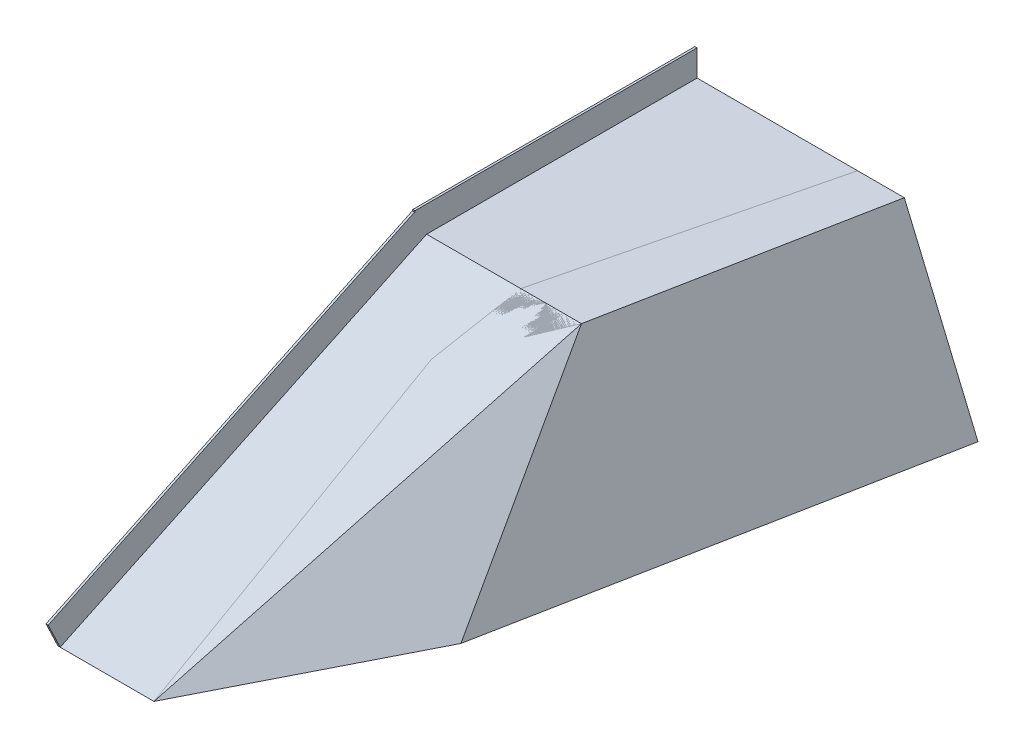
SolidWorks part; units mm, degrees
ref_plane "Front Plane" through (0, 0, 0) normal (0, 0, 1) x (1, 0, 0)
ref_plane "Top Plane" through (0, 0, 0) normal (0, 1, 0) x (1, 0, 0)
ref_plane "Right Plane" through (0, 0, 0) normal (1, 0, 0) x (0, 0, -1)
sketch "Sketch1" plane through (0, 0, 0) normal (0, 1, 0) x (1, 0, 0)
  line L0 (0, 1066.8) -> (0, 0)
  line L1 (0, 0) -> (279.4, 0)
  line L2 (279.4, 0) -> (457.2, 1066.8)
  line L3 (457.2, 1066.8) -> (0, 1066.8)
  dimension "D1" = 279.4
  dimension "D2" = 457.2
  dimension "D3" = 1066.8
extrude "Boss-Extrude1" add sketch "Sketch1" along normal blind 508
sketch "Sketch2" plane through (0, 0, 0) normal (-1, 0, 0) x (0, 0, 1)
  line L0 (0, 0) -> (-1066.8, 508)
  line L1 (-1066.8, 508) -> (-1066.8, 732.6724)
  line L2 (-1066.8, 732.6724) -> (0, 732.6724)
  line L3 (0, 732.6724) -> (0, 0)
extrude "Cut-Extrude1" cut sketch "Sketch2" against normal blind 508
sketch "Sketch3" plane through (0, 0, 0) normal (0, -1, 0) x (1, 0, 0)
  line L0 (0, -1066.8) -> (0, -1854.2)
  line L1 (0, -1854.2) -> (609.6, -1854.2)
  line L2 (609.6, -1854.2) -> (457.2, -1066.8)
  line L3 (457.2, -1066.8) -> (0, -1066.8)
  dimension "D1" = 787.4
  dimension "D2" = 609.6
extrude "Boss-Extrude2" add sketch "Sketch3" against normal blind 508
ref_point "Point1"
sketch "Sketch4" plane through (0, 0, 0) normal (0, -1, 0) x (1, 0, 0)
  line L0 (279.4, 0) -> (758.0246, -943.9298)
  line L1 (758.0246, -943.9298) -> (824.1633, -1854.2)
  line L2 (824.1633, -1854.2) -> (609.6, -1854.2)
  line L4 (609.6, -1854.2) -> (473.6054, -1854.2)
  line L5 (473.6054, -1854.2) -> (229.3242, -858.0039)
  line L6 (229.3242, -858.0039) -> (279.4, 0)
extrude "Boss-Extrude3" add sketch "Sketch4" against normal blind 635 separate body
ref_plane "Plane1" through (158.0257, 112.9593, 80.1278) normal (-0.7521, -0.5376, -0.3813) x (-0.3102, -0.2218, 0.9244)
sketch "Sketch5" plane through (158.0257, 112.9593, 80.1278) normal (-0.7521, -0.5376, -0.3813) x (-0.3102, -0.2218, 0.9244)
  line L0 (-393.6646, 703.6256) -> (953.2419, -176.9288)
  line L1 (953.2419, -176.9288) -> (-1326.8428, -923.5564)
  line L2 (-1326.8428, -923.5564) -> (-2274.7883, -628.3267)
  line L3 (-2274.7883, -628.3267) -> (-2325.5283, 172.3758)
  line L4 (-2325.5283, 172.3758) -> (-393.6646, 703.6256)
extrude "Cut-Extrude3" cut sketch "Sketch5" against normal blind 1016
ref_plane "Plane2" through (397.9401, 254.279, 77.0207) normal (0.8317, 0.5314, 0.161) x (0.1356, 0.0867, -0.987)
sketch "Sketch6" plane through (397.9401, 254.279, 77.0207) normal (0.8317, 0.5314, 0.161) x (0.1356, 0.0867, -0.987)
  line L0 (1082.533, 1261.8546) -> (2538.8005, 767.6885)
  line L1 (2538.8005, 767.6885) -> (2437.6041, -1113.0464)
  line L2 (2437.6041, -1113.0464) -> (306.9995, -1023.5801)
  line L3 (306.9995, -1023.5801) -> (1082.533, 1261.8546)
extrude "Cut-Extrude6" cut sketch "Sketch6" along normal blind 508
sketch "Sketch7" plane through (0, 0, 0) normal (0, 0.9029, 0.4299) x (1, 0, 0)
  line L0 (0, 1181.5779) -> (0, 0)
  line L1 (0, 0) -> (1197.0459, 0)
  line L2 (1197.0459, 0) -> (1543.8795, 955.9278)
  line L3 (1543.8795, 955.9278) -> (976.3528, 2301.292)
  line L4 (976.3528, 2301.292) -> (0, 1181.5779)
extrude "Cut-Extrude7" cut sketch "Sketch7" along normal blind 1016
ref_plane "Plane3" through (382.6816, 161.6328, 74.0674) normal (0.9069, 0.383, 0.1755) x (0.1617, 0.0683, -0.9845)
sketch "Sketch8" plane through (382.6816, 161.6328, 74.0674) normal (0.9069, 0.383, 0.1755) x (0.1617, 0.0683, -0.9845)
  line L0 (1197.5568, 999.1439) -> (2455.296, 323.4977)
  line L1 (2455.296, 323.4977) -> (2410.7054, -956.0431)
  line L2 (2410.7054, -956.0431) -> (776.2886, -956.0431)
  line L3 (776.2886, -956.0431) -> (430.3512, -503.2752)
  line L4 (430.3512, -503.2752) -> (1197.5568, 999.1439)
extrude "Cut-Extrude8" cut sketch "Sketch8" along normal blind 1016
sketch "Sketch9" plane through (0, 508, 0) normal (0, 1, 0) x (1, 0, 0)
  line L0 (351.5224, 2301.2259) -> (1863.402, 1800.0992)
  line L1 (1863.402, 1800.0992) -> (1313.9442, 629.1947)
  line L2 (1313.9442, 629.1947) -> (-286.9383, 375.0155)
  line L3 (-286.9383, 375.0155) -> (-444.0043, 1364.2557)
  line L4 (-444.0043, 1364.2557) -> (351.5224, 2301.2259)
extrude "Cut-Extrude9" cut sketch "Sketch9" along normal blind 1016
sketch "Sketch10" plane through (0, 508, 0) normal (0, 1, 0) x (1, 0, 0)
  line L1 (0, 1854.2) -> (6.35, 1854.2)
  line L2 (0, 1854.2) -> (0, 1032.7207)
  line L3 (0, 1032.7207) -> (6.35, 1032.7207)
  line L4 (6.35, 1854.2) -> (6.35, 1032.7207)
  point P5 (0, 0)
  dimension "D1" = 6.35
extrude "Boss-Extrude4" add sketch "Sketch10" along normal blind 76.2
sketch "Sketch11" plane through (0, 0, 0) normal (0, 0.9029, 0.4299) x (1, 0, 0)
  line L0 (0, 0) -> (279.4, 0) construction
  line L1 (0, 1181.5779) -> (6.35, 1181.5779)
  line L2 (0, 1181.5779) -> (0, 0)
  line L3 (0, 0) -> (6.35, 0)
  line L4 (6.35, 1181.5779) -> (6.35, 0)
  dimension "D1" = 6.35
extrude "Boss-Extrude6" add sketch "Sketch11" along normal blind 81.28
